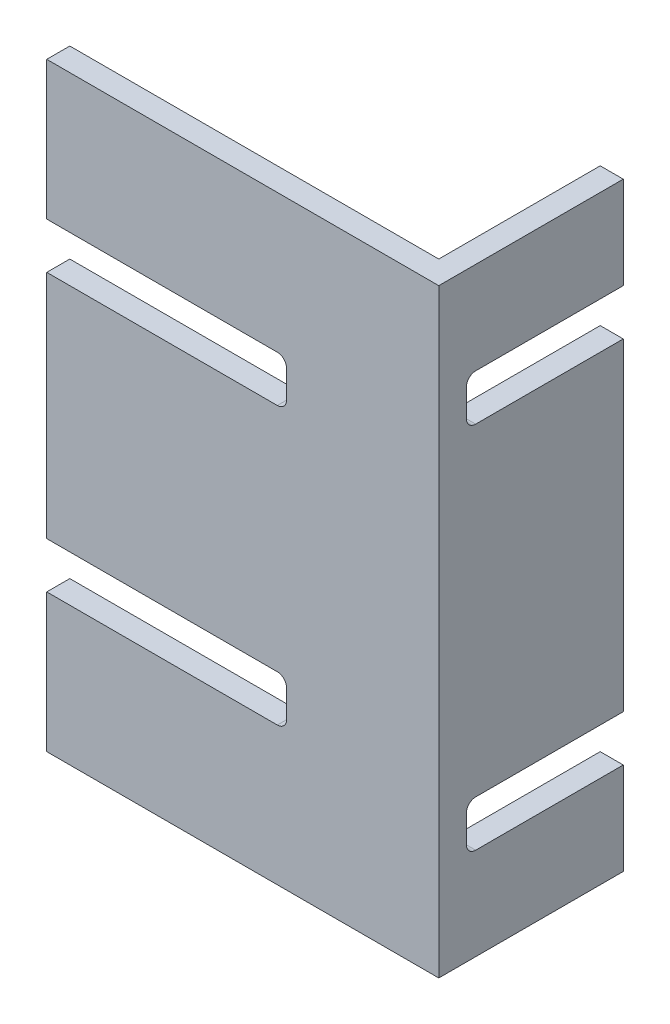
SolidWorks part; units mm, degrees
ref_plane "Front Plane" through (0, 0, 0) normal (0, 0, 1) x (1, 0, 0)
ref_plane "Top Plane" through (0, 0, 0) normal (0, 1, 0) x (1, 0, 0)
ref_plane "Right Plane" through (0, 0, 0) normal (1, 0, 0) x (0, 0, -1)
sketch "Sketch1" plane through (0, 0, 0) normal (0, 1, 0) x (1, 0, 0)
  line L0 (-95.3402, -23.7075) -> (-15.3402, -23.7075)
  line L1 (-15.3402, -23.7075) -> (-15.3402, 11.2925)
  line L2 (-15.3402, 11.2925) -> (-10.3402, 11.2925)
  line L3 (-10.3402, 11.2925) -> (-10.3402, -28.7075)
  line L4 (-10.3402, -28.7075) -> (-95.3402, -28.7075)
  line L5 (-95.3402, -28.7075) -> (-95.3402, -23.7075)
  dimension "D1" = 5
  dimension "D2" = 5
  dimension "D3" = 80
  dimension "D4" = 35
extrude "Boss-Extrude1" add sketch "Sketch1" along normal blind 130
ref_plane "Plane1" through (-15.3402, 0, 0) normal (-1, 0, 0) x (0, 0, 1)
sketch "Sketch2" plane through (-15.3402, 0, 0) normal (-1, 0, 0) x (0, 0, 1)
  line L0 (-11.2925, 130) -> (-11.2925, 0) construction
  line L1 (-11.2925, 110) -> (20.7075, 110)
  line L2 (-11.2925, 110) -> (-11.2925, 100)
  line L3 (-11.2925, 100) -> (20.7075, 100)
  line L4 (22.7075, 108) -> (22.7075, 102)
  line L5 (-11.2925, 130) -> (23.7075, 130) construction
  line L6 (-11.2925, 30) -> (20.7075, 30)
  line L7 (-11.2925, 30) -> (-11.2925, 20)
  line L8 (-11.2925, 20) -> (20.7075, 20)
  line L9 (22.7075, 28) -> (22.7075, 22)
  line L10 (-11.2925, 0) -> (23.7075, 0) construction
  arc A0 (22.7075, 102) -> (20.7075, 100) centre (20.7075, 102) cw
  arc A1 (22.7075, 108) -> (20.7075, 110) centre (20.7075, 108) ccw
  arc A2 (22.7075, 22) -> (20.7075, 20) centre (20.7075, 22) cw
  arc A3 (22.7075, 28) -> (20.7075, 30) centre (20.7075, 28) ccw
  dimension "D5" = 2
  dimension "D1" = 20
  dimension "D2" = 10
  dimension "D3" = 20
  dimension "D4" = 10
extrude "Cut-Extrude1" cut sketch "Sketch2" against normal blind 10
ref_plane "Plane2" through (0, 0, 23.7075) normal (0, 0, -1) x (-1, 0, 0)
sketch "Sketch3" plane through (0, 0, 23.7075) normal (0, 0, -1) x (-1, 0, 0)
  line L0 (95.3402, 130) -> (95.3402, 0) construction
  line L1 (95.3402, 100) -> (45.3402, 100)
  line L2 (95.3402, 100) -> (95.3402, 90)
  line L3 (95.3402, 90) -> (45.3402, 90)
  line L4 (43.3402, 98) -> (43.3402, 92)
  line L5 (15.3402, 130) -> (95.3402, 130) construction
  line L6 (95.3402, 40) -> (45.3402, 40)
  line L7 (95.3402, 40) -> (95.3402, 30)
  line L8 (95.3402, 30) -> (45.3402, 30)
  line L9 (43.3402, 38) -> (43.3402, 32)
  line L10 (15.3402, 0) -> (95.3402, 0) construction
  arc A0 (43.3402, 32) -> (45.3402, 30) centre (45.3402, 32) ccw
  arc A1 (43.3402, 38) -> (45.3402, 40) centre (45.3402, 38) cw
  arc A2 (43.3402, 92) -> (45.3402, 90) centre (45.3402, 92) ccw
  arc A3 (43.3402, 98) -> (45.3402, 100) centre (45.3402, 98) cw
  dimension "D5" = 2
  dimension "D1" = 30
  dimension "D2" = 10
  dimension "D3" = 30
  dimension "D4" = 10
extrude "Cut-Extrude2" cut sketch "Sketch3" against normal blind 10
